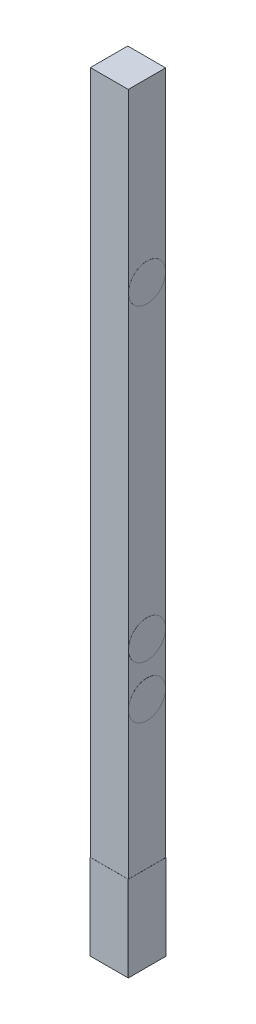
SolidWorks part; units mm, degrees
material "Alloy Steel"
ref_plane "Front Plane" through (0, 0, 0) normal (0, 0, 1) x (1, 0, 0)
ref_plane "Top Plane" through (0, 0, 0) normal (0, 1, 0) x (1, 0, 0)
ref_plane "Right Plane" through (0, 0, 0) normal (1, 0, 0) x (0, 0, -1)
sketch "Sketch1" plane through (0, 0, 0) normal (0, 1, 0) x (1, 0, 0)
  line L1 (-22.51, -22.1884) -> (22.51, -22.1884)
  line L2 (-22.51, -22.1884) -> (-22.51, 22.1884)
  line L3 (-22.51, 22.1884) -> (22.51, 22.1884)
  line L4 (22.51, -22.1884) -> (22.51, 22.1884)
  line L5 (-22.51, -22.1884) -> (22.51, 22.1884) construction
  line L6 (-22.51, 22.1884) -> (22.51, -22.1884) construction
  point P0 (0, 0)
  dimension "D1" = 45.02
extrude "Boss-Extrude1" add sketch "Sketch1" along normal blind 914.4
sketch "Sketch2" plane through (22.51, 0, 0) normal (1, 0, 0) x (0, 0, -1)
  line L0 (-22.1884, 0) -> (22.1884, 0) construction
  line L3 (22.1884, 914.4) -> (22.1884, 0) construction
  circle A0 centre (0, 275.7) radius 22
  circle A1 centre (0, 337.8) radius 22
  circle A2 centre (0, 704.8) radius 22
  point P0 (0, 275.7)
  dimension "D3" = 44
  dimension "D4" = 44
  dimension "D5" = 44
  dimension "D6" = 367
  dimension "D7" = 62.1
  dimension "D1" = 275.7
  dimension "D2" = 22.1884
extrude "Boss-Extrude2" add sketch "Sketch2" along normal blind 0.1
sketch "Sketch3" plane through (22.51, 0, 0) normal (1, 0, 0) x (0, 0, -1)
  line L0 (-22.1884, 0) -> (22.1884, 0) construction
  line L1 (-22.1884, 0) -> (22.1884, 0)
  line L2 (-22.1884, 0) -> (-22.1884, 101.6)
  line L3 (-22.1884, 101.6) -> (22.1884, 101.6)
  line L4 (22.1884, 0) -> (22.1884, 101.6)
  line L5 (22.1884, 914.4) -> (22.1884, 0) construction
  dimension "D1" = 101.6
extrude "Boss-Extrude3" add sketch "Sketch3" along normal blind 0.1
sketch "Sketch4" plane through (0, 0, -22.1884) normal (0, 0, -1) x (-1, 0, 0)
  line L0 (22.51, 914.4) -> (22.51, 0) construction
  line L1 (-22.61, 0) -> (22.51, 0)
  line L2 (-22.61, 0) -> (-22.61, 101.6)
  line L3 (-22.61, 101.6) -> (22.51, 101.6)
  line L4 (22.51, 0) -> (22.51, 101.6)
  dimension "D1" = 101.6
extrude "Boss-Extrude4" add sketch "Sketch4" along normal blind 0.1
sketch "Sketch5" plane through (-22.51, 0, 0) normal (-1, 0, 0) x (0, 0, 1)
  line L0 (22.1884, 914.4) -> (22.1884, 0) construction
  line L1 (-22.2884, 0) -> (22.1884, 0)
  line L2 (-22.2884, 0) -> (-22.2884, 101.6)
  line L3 (-22.2884, 101.6) -> (22.1884, 101.6)
  line L4 (22.1884, 0) -> (22.1884, 101.6)
  dimension "D1" = 101.6
extrude "Boss-Extrude5" add sketch "Sketch5" along normal blind 0.1
sketch "Sketch6" plane through (0, 0, 22.1884) normal (0, 0, 1) x (1, 0, 0)
  line L0 (22.51, 914.4) -> (22.51, 101.6) construction
  line L1 (-22.61, 0) -> (22.51, 0)
  line L2 (-22.61, 0) -> (-22.61, 101.6)
  line L3 (-22.61, 101.6) -> (22.51, 101.6)
  line L4 (22.51, 0) -> (22.51, 101.6)
  dimension "D1" = 101.6
extrude "Boss-Extrude6" add sketch "Sketch6" along normal blind 0.1
